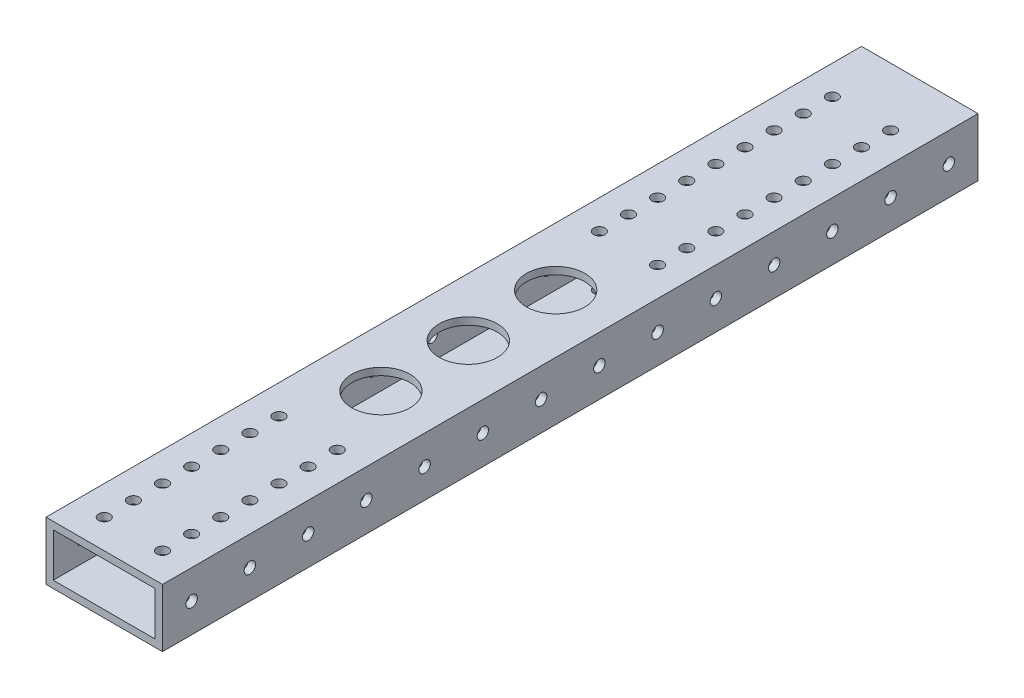
SolidWorks part; units mm, degrees
material "6061-T6 (SS)"
ref_plane "Front Plane" through (0, 0, 0) normal (0, 0, 1) x (1, 0, 0)
ref_plane "Top Plane" through (0, 0, 0) normal (0, 1, 0) x (1, 0, 0)
ref_plane "Right Plane" through (0, 0, 0) normal (1, 0, 0) x (0, 0, -1)
sketch "Sketch1" plane through (0, 0, 0) normal (0, 0, 1) x (1, 0, 0)
  line L0 (-22.225, 9.525) -> (22.225, 9.525)
  line L1 (-25.4, 12.7) -> (25.4, 12.7)
  line L2 (-25.4, 12.7) -> (-25.4, -12.7)
  line L3 (-25.4, -12.7) -> (25.4, -12.7)
  line L4 (25.4, 12.7) -> (25.4, -12.7)
  line L5 (22.225, 9.525) -> (22.225, -9.525)
  line L6 (-22.225, -9.525) -> (22.225, -9.525)
  line L7 (-22.225, 9.525) -> (-22.225, -9.525)
  line L8 (-25.4, 12.7) -> (25.4, -12.7) construction
  line L9 (25.4, 12.7) -> (-25.4, -12.7) construction
  point P5 (0, 0)
  dimension "D1" = 50.8
  dimension "D2" = 25.4
  dimension "D3" = 3.175
extrude "Boss-Extrude1" add sketch "Sketch1" along normal mid plane 355.6
sketch "Sketch2" plane through (0, 12.7, 0) normal (0, -1, 0) x (1, 0, 0)
  circle A36 centre (-12.7, 165.1) radius 2.4892 construction
  circle A37 centre (-12.7, 152.4) radius 2.4892 construction
  circle A38 centre (-12.7, 139.7) radius 2.4892 construction
  circle A39 centre (-12.7, 127) radius 2.4892 construction
  circle A40 centre (-12.7, 114.3) radius 2.4892 construction
  circle A41 centre (-12.7, 101.6) radius 2.4892 construction
  circle A42 centre (-12.7, 88.9) radius 2.4892 construction
  circle A50 centre (12.7, 165.1) radius 2.4892 construction
  circle A51 centre (12.7, 152.4) radius 2.4892 construction
  circle A52 centre (12.7, 139.7) radius 2.4892 construction
  circle A53 centre (12.7, 127) radius 2.4892 construction
  circle A54 centre (12.7, 114.3) radius 2.4892 construction
  circle A55 centre (12.7, 101.6) radius 2.4892 construction
  circle A56 centre (12.7, 88.9) radius 2.4892 construction
  circle A57 centre (-12.7, 165.1) radius 2.4892
  circle A58 centre (-12.7, 152.4) radius 2.4892
  circle A59 centre (-12.7, 139.7) radius 2.4892
  circle A60 centre (-12.7, 127) radius 2.4892
  circle A61 centre (-12.7, 114.3) radius 2.4892
  circle A62 centre (-12.7, 101.6) radius 2.4892
  circle A63 centre (-12.7, 88.9) radius 2.4892
  circle A71 centre (12.7, 165.1) radius 2.4892
  circle A72 centre (12.7, 152.4) radius 2.4892
  circle A73 centre (12.7, 139.7) radius 2.4892
  circle A74 centre (12.7, 127) radius 2.4892
  circle A75 centre (12.7, 114.3) radius 2.4892
  circle A76 centre (12.7, 101.6) radius 2.4892
  circle A77 centre (12.7, 88.9) radius 2.4892
extrude "Cut-Extrude1" cut sketch "Sketch2" along normal up to next
sketch "Sketch3" plane through (25.4, 0, 0) normal (1, 0, 0) x (0, 0, -1)
  line L0 (-177.8, 0) -> (177.8, 0) construction
  line L1 (-177.8, -12.7) -> (-177.8, 12.7) construction
  line L2 (177.8, -12.7) -> (177.8, 12.7) construction
  circle A0 centre (-165.1, 0) radius 2.4892
  circle A1 centre (-139.7, 0) radius 2.4892
  circle A2 centre (-114.3, 0) radius 2.4892
  circle A3 centre (-88.9, 0) radius 2.4892
  circle A4 centre (-63.5, 0) radius 2.4892
  circle A5 centre (-38.1, 0) radius 2.4892
  circle A6 centre (-12.7, 0) radius 2.4892
  circle A7 centre (12.7, 0) radius 2.4892
  circle A8 centre (38.1, 0) radius 2.4892
  circle A9 centre (63.5, 0) radius 2.4892
  circle A10 centre (88.9, 0) radius 2.4892
  circle A11 centre (114.3, 0) radius 2.4892
  circle A12 centre (139.7, 0) radius 2.4892
  circle A13 centre (165.1, 0) radius 2.4892
  dimension "D1" = 4.9784
  dimension "D2" = 12.7
  dimension "D4" = 25.4
  dimension "D3" = 14
extrude "Cut-Extrude2" cut sketch "Sketch3" against normal through all
sketch "Sketch4" plane through (0, -12.7, 0) normal (0, -1, 0) x (1, 0, 0)
  circle A0 centre (-12.7, -152.4) radius 2.4892 construction
  circle A1 centre (-12.7, -139.7) radius 2.4892 construction
  circle A2 centre (-12.7, -127) radius 2.4892 construction
  circle A3 centre (-12.7, -114.3) radius 2.4892 construction
  circle A4 centre (-12.7, -101.6) radius 2.4892 construction
  circle A5 centre (-12.7, -88.9) radius 2.4892 construction
  circle A6 centre (-12.7, -76.2) radius 2.4892 construction
  circle A7 centre (-12.7, -63.5) radius 2.4892 construction
  circle A8 centre (-12.7, -50.8) radius 2.4892 construction
  circle A9 centre (12.7, -50.8) radius 2.4892 construction
  circle A10 centre (12.7, -63.5) radius 2.4892 construction
  circle A11 centre (12.7, -76.2) radius 2.4892 construction
  circle A12 centre (12.7, -88.9) radius 2.4892 construction
  circle A13 centre (12.7, -101.6) radius 2.4892 construction
  circle A14 centre (12.7, -114.3) radius 2.4892 construction
  circle A15 centre (12.7, -127) radius 2.4892 construction
  circle A16 centre (12.7, -139.7) radius 2.4892 construction
  circle A17 centre (12.7, -152.4) radius 2.4892 construction
  circle A18 centre (-12.7, -152.4) radius 2.4892
  circle A19 centre (-12.7, -139.7) radius 2.4892
  circle A20 centre (-12.7, -127) radius 2.4892
  circle A21 centre (-12.7, -114.3) radius 2.4892
  circle A22 centre (-12.7, -101.6) radius 2.4892
  circle A23 centre (-12.7, -88.9) radius 2.4892
  circle A24 centre (-12.7, -76.2) radius 2.4892
  circle A25 centre (-12.7, -63.5) radius 2.4892
  circle A26 centre (-12.7, -50.8) radius 2.4892
  circle A27 centre (12.7, -50.8) radius 2.4892
  circle A28 centre (12.7, -63.5) radius 2.4892
  circle A29 centre (12.7, -76.2) radius 2.4892
  circle A30 centre (12.7, -88.9) radius 2.4892
  circle A31 centre (12.7, -101.6) radius 2.4892
  circle A32 centre (12.7, -114.3) radius 2.4892
  circle A33 centre (12.7, -127) radius 2.4892
  circle A34 centre (12.7, -139.7) radius 2.4892
  circle A35 centre (12.7, -152.4) radius 2.4892
extrude "Cut-Extrude3" cut sketch "Sketch4" against normal through all
sketch "Sketch5" plane through (0, 12.7, 0) normal (0, 1, 0) x (1, 0, 0)
  line L0 (0, 177.8) -> (0, -177.8) construction
  line L1 (25.4, 177.8) -> (-25.4, 177.8) construction
  line L2 (25.4, -177.8) -> (-25.4, -177.8) construction
  circle A0 centre (0, -57.15) radius 12.7
  circle A1 centre (0, -19.05) radius 12.7
  circle A2 centre (0, 19.05) radius 12.7
  dimension "D1" = 25.4
  dimension "D2" = 38.1
  dimension "D3" = 38.1
  dimension "D4" = 120.65
extrude "Cut-Extrude4" cut sketch "Sketch5" against normal through all
